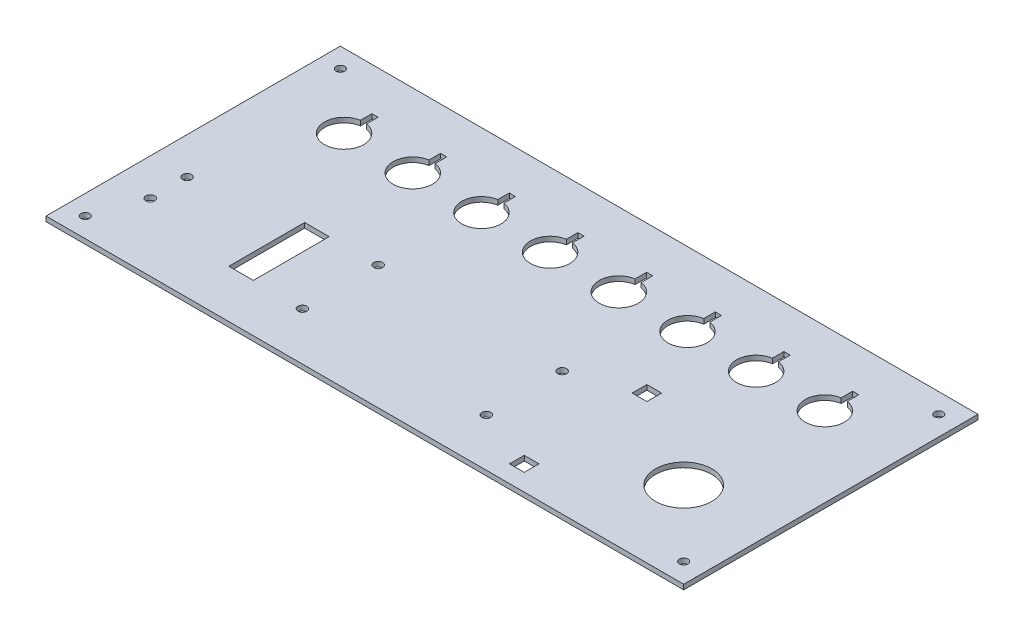
SolidWorks part; units mm, degrees
ref_plane "前基準面" through (0, 0, 0) normal (0, 0, 1) x (1, 0, 0)
ref_plane "上基準面" through (0, 0, 0) normal (0, 1, 0) x (1, 0, 0)
ref_plane "右基準面" through (0, 0, 0) normal (1, 0, 0) x (0, 0, -1)
sketch "草圖1" plane through (0, 0, 0) normal (0, 1, 0) x (1, 0, 0)
  line L0 (-98.461, 30) -> (98.461, 30) construction
  line L1 (-130, 60) -> (130, 60)
  line L2 (-130, 60) -> (-130, -60)
  line L3 (-130, -60) -> (130, -60)
  line L4 (130, 60) -> (130, -60)
  line L5 (-130, 60) -> (130, -60) construction
  line L6 (-130, -60) -> (130, 60) construction
  line L11 (-107.2683, 41.9969) -> (-89.6514, 18) construction
  line L12 (-107.6514, 18) -> (-89.2683, 42.0029) construction
  line L13 (-61, 42) -> (-61, 18) construction
  line L14 (-79, 42) -> (-61, 42) construction
  line L15 (-79, 42) -> (-79, 18) construction
  line L16 (-79, 18) -> (-61, 18) construction
  line L17 (-33, 42) -> (-33, 18) construction
  line L18 (-51, 42) -> (-33, 42) construction
  line L19 (-51, 42) -> (-51, 18) construction
  line L20 (-51, 18) -> (-33, 18) construction
  line L21 (-5, 42) -> (-5, 18) construction
  line L22 (-23, 42) -> (-5, 42) construction
  line L23 (-23, 42) -> (-23, 18) construction
  line L24 (-23, 18) -> (-5, 18) construction
  line L25 (23, 42) -> (23, 18) construction
  line L26 (5, 42) -> (23, 42) construction
  line L27 (5, 42) -> (5, 18) construction
  line L28 (5, 18) -> (23, 18) construction
  line L29 (51, 42) -> (51, 18) construction
  line L30 (33, 42) -> (51, 42) construction
  line L31 (33, 42) -> (33, 18) construction
  line L32 (33, 18) -> (51, 18) construction
  line L33 (79, 42) -> (79, 18) construction
  line L34 (61, 42) -> (79, 42) construction
  line L35 (61, 42) -> (61, 18) construction
  line L36 (61, 18) -> (79, 18) construction
  line L37 (107.6514, 42) -> (107.6514, 18.0053) construction
  line L38 (89.6514, 42) -> (107.6514, 42) construction
  line L39 (89.6514, 42) -> (89.2706, 17.9947) construction
  line L40 (89.2706, 17.9947) -> (107.6514, 18.0053) construction
  line L41 (-99.0992, -25) -> (112.2012, -25) construction
  line L42 (-75, -9.55) -> (-65, -9.55)
  line L43 (-75, -9.55) -> (-75, -40.45)
  line L44 (-75, -40.45) -> (-65, -40.45)
  line L45 (-65, -9.55) -> (-65, -40.45)
  line L46 (-45, -9.55) -> (30, -9.55) construction
  line L47 (-45, -9.55) -> (-45, -40.45) construction
  line L48 (-45, -40.45) -> (30, -40.45) construction
  line L49 (30, -9.55) -> (30, -40.45) construction
  line L50 (58, -53) -> (58, -47)
  line L51 (52, 3) -> (58, 3)
  line L52 (52, 3) -> (52, -3)
  line L53 (52, -3) -> (58, -3)
  line L54 (58, 3) -> (58, -3)
  line L55 (52, -53) -> (58, -53)
  line L56 (52, -53) -> (52, -47)
  line L57 (52, -47) -> (58, -47)
  line L58 (-75, -25) -> (-45, -25) construction
  line L59 (0, 30) -> (0, 60) construction
  line L60 (98.461, 18) -> (98.461, 30) construction
  line L61 (-98.461, 37.5967) -> (-98.461, 42.5967) construction
  line L62 (-122, 52) -> (122, 52) construction
  line L63 (-122, 52) -> (-122, -52) construction
  line L64 (-122, -52) -> (122, -52) construction
  line L65 (122, 52) -> (122, -52) construction
  line L66 (-122, 52) -> (122, -52) construction
  line L67 (-122, -52) -> (122, 52) construction
  line L68 (-71.711, 42.5967) -> (-69.211, 42.5967)
  line L69 (-99.711, 42.5967) -> (-97.211, 42.5967)
  line L70 (-99.711, 42.5967) -> (-99.711, 37.9017)
  line L72 (-97.211, 42.5967) -> (-97.211, 37.9017)
  line L73 (-99.711, 42.5967) -> (-97.3756, 37.926) construction
  line L74 (-99.711, 37.5967) -> (-97.211, 42.5967) construction
  line L75 (-69.211, 42.5967) -> (-69.211, 37.9017)
  line L76 (-71.711, 42.5967) -> (-71.711, 37.9017)
  line L77 (-43.711, 42.5967) -> (-41.211, 42.5967)
  line L78 (-41.211, 42.5967) -> (-41.211, 37.9017)
  line L79 (-43.711, 42.5967) -> (-43.711, 37.9017)
  line L80 (-15.711, 42.5967) -> (-13.211, 42.5967)
  line L81 (-13.211, 42.5967) -> (-13.211, 37.9017)
  line L82 (-15.711, 42.5967) -> (-15.711, 37.9017)
  line L83 (12.289, 42.5967) -> (14.789, 42.5967)
  line L84 (14.789, 42.5967) -> (14.789, 37.9017)
  line L85 (12.289, 42.5967) -> (12.289, 37.9017)
  line L86 (40.289, 42.5967) -> (42.789, 42.5967)
  line L87 (42.789, 42.5967) -> (42.789, 37.9017)
  line L88 (40.289, 42.5967) -> (40.289, 37.9017)
  line L89 (68.289, 42.5967) -> (70.789, 42.5967)
  line L90 (70.789, 42.5967) -> (70.789, 37.9017)
  line L91 (68.289, 42.5967) -> (68.289, 37.9017)
  line L92 (96.289, 42.5967) -> (98.789, 42.5967)
  line L93 (98.789, 42.5967) -> (98.789, 37.9017)
  line L94 (96.289, 42.5967) -> (96.289, 37.9017)
  line L95 (-115, -17.5) -> (-115, -37.1141) construction
  circle A0 centre (-45, -9.55) radius 1.8
  circle A1 centre (-45, -40.45) radius 1.8
  circle A2 centre (30, -9.55) radius 1.8
  circle A3 centre (30, -40.45) radius 1.8
  circle A4 centre (95, -25) radius 11.5
  circle A5 centre (-122, 52) radius 1.75
  circle A6 centre (-122, -52) radius 1.75
  circle A7 centre (122, 52) radius 1.75
  circle A8 centre (122, -52) radius 1.75
  arc A9 (-99.711, 37.9017) -> (-97.211, 37.9017) centre (-98.461, 30) ccw
  arc A10 (-71.711, 37.9017) -> (-69.211, 37.9017) centre (-70.461, 30) ccw
  arc A11 (-43.711, 37.9017) -> (-41.211, 37.9017) centre (-42.461, 30) ccw
  arc A12 (-15.711, 37.9017) -> (-13.211, 37.9017) centre (-14.461, 30) ccw
  arc A13 (12.289, 37.9017) -> (14.789, 37.9017) centre (13.539, 30) ccw
  arc A14 (40.289, 37.9017) -> (42.789, 37.9017) centre (41.539, 30) ccw
  arc A15 (68.289, 37.9017) -> (70.789, 37.9017) centre (69.539, 30) ccw
  arc A16 (96.289, 37.9017) -> (98.789, 37.9017) centre (97.539, 30) ccw
  circle A17 centre (-115, -17.5) radius 1.8
  circle A18 centre (-115, -32.5) radius 1.8
  point P0 (0, 0)
  point P6 (-98.461, 30)
  point P66 (0, 0)
  point P80 (-98.461, 40.0967)
  dimension "D10" = 6
  dimension "D15" = 35
  dimension "D5" = 16
  dimension "D20" = 23
  dimension "D1" = 260
  dimension "D2" = 120
  dimension "D3" = 24
  dimension "D4" = 18
  dimension "D6" = 30.9
  dimension "D7" = 10
  dimension "D8" = 75
  dimension "D9" = 30.9
  dimension "D11" = 6
  dimension "D12" = 22
  dimension "D13" = 8
  dimension "D14" = 8
  dimension "D16" = 30
  dimension "D17" = 2.5
  dimension "D18" = 5
  dimension "D21" = 35
  dimension "D22" = 72
  dimension "D23" = 100
  dimension "D24" = 20
  dimension "D25" = 7.5
  dimension "D27" = 40
  dimension "D19" = 8
extrude "填料-伸長1" add sketch "草圖1" along normal blind 2
